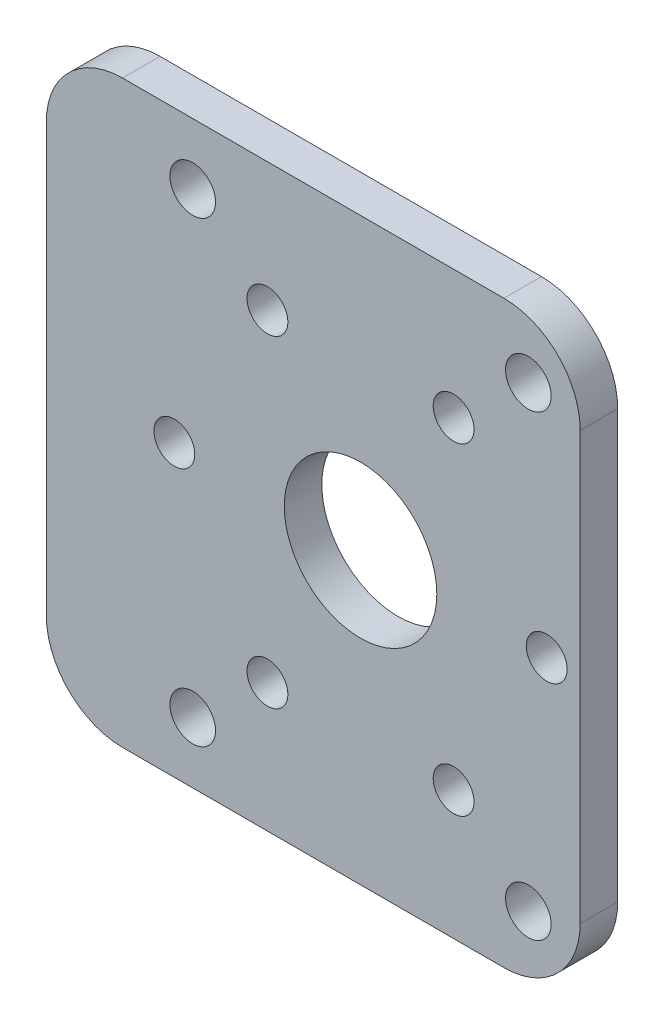
SolidWorks part; units mm, degrees
ref_plane "Front Plane" through (0, 0, 0) normal (0, 0, 1) x (1, 0, 0)
ref_plane "Top Plane" through (0, 0, 0) normal (0, 1, 0) x (1, 0, 0)
ref_plane "Right Plane" through (0, 0, 0) normal (1, 0, 0) x (0, 0, -1)
sketch "Sketch1" plane through (0, 0, 0) normal (0, 0, 1) x (1, 0, 0)
  line L1 (69.85, 48.26) -> (114.3, 48.26)
  line L2 (69.85, 48.26) -> (69.85, 0)
  line L3 (69.85, 0) -> (114.3, 0)
  line L4 (114.3, 48.26) -> (114.3, 0)
  dimension "D1" = 48.26
  dimension "D2" = 44.45
extrude "Boss-Extrude1" add sketch "Sketch1" along normal blind 3.1242
fillet "Fillet1" radius 6.35 4 edges at (114.3, 48.26, 1.5621) (114.3, 0, 1.5621) (69.85, 0, 1.5621) (69.85, 48.26, 1.5621)
hole_wizard "#6 Clearance Hole1" positions "Sketch2" profile "Sketch3" hole size "#6" standard "ANSI Inch"
sketch "Sketch2" plane through (0, 0, 3.1242) normal (0, 0, 1) x (1, 0, 0)
  line L0 (82.042, 43.18) -> (109.982, 43.18) construction
  line L1 (109.982, 43.18) -> (109.982, 5.08) construction
  line L2 (109.982, 5.08) -> (82.042, 5.08) construction
  line L3 (82.042, 5.08) -> (82.042, 43.18) construction
  line L5 (107.95, 48.26) -> (76.2, 48.26) construction
  line L6 (69.85, 41.91) -> (69.85, 6.35) construction
  point P0 (82.042, 43.18)
  point P3 (109.982, 43.18)
  point P6 (109.982, 5.08)
  point P9 (82.042, 5.08)
  point P30 (0, 0)
  point P31 (0, 0)
  point P32 (0, 0)
  point P33 (0, 0)
  dimension "D1" = 38.1
  dimension "D2" = 27.94
  dimension "D3" = 5.08
  dimension "D4" = 12.192
sketch "Sketch3" plane through (82.042, 43.18, 3.1242) normal (1, 0, 0) x (0, -1, 0)
  line L0 (0, 0) -> (0, 6.2208)
  line L1 (0, 6.2208) -> (1.8986, 5.08)
  line L2 (1.8986, 5.08) -> (1.8986, 0)
  line L5 (1.8986, 0) -> (0, 0)
  line L10 (0, 6.2208) -> (-1.8987, 5.08) construction
  line L11 (0, -6.35) -> (0, 107.95) construction
  dimension "Hole Dia." = 3.7973
  dimension "Hole Depth" = 5.08
  dimension "Drill Angle" = 118
sketch "Sketch4" plane through (0, 0, 3.1242) normal (0, 0, 1) x (1, 0, 0)
  line L0 (76.2, 0) -> (107.95, 0) construction
  line L1 (69.85, 41.91) -> (69.85, 6.35) construction
  circle A0 centre (96.012, 24.13) radius 6.35
  point P7 (0, 0)
  dimension "D1" = 12.7
  dimension "D2" = 24.13
  dimension "D3" = 26.162
extrude "Cut-Extrude1" cut sketch "Sketch4" against normal through all
hole_wizard "M3 Clearance Hole1" positions "Sketch5" profile "Sketch6" hole size "M3" standard "ANSI Metric" end condition through all
sketch "Sketch5" plane through (0, 0, 3.1242) normal (0, 0, 1) x (1, 0, 0)
  line L0 (96.012, 24.13) -> (111.512, 24.13) construction
  point P0 (111.512, 24.13)
  point P13 (103.762, 10.7066)
  point P14 (88.262, 10.7066)
  point P15 (80.512, 24.13)
  point P16 (88.262, 37.5534)
  point P17 (103.762, 37.5534)
  point P18 (96.012, 24.13)
  dimension "D1" = 15.5
  dimension "D2" = 6
sketch "Sketch6" plane through (111.512, 24.13, 3.1242) normal (1, 0, 0) x (0, -1, 0)
  line L0 (0, 0) -> (0, 3.1242)
  line L1 (0, 3.1242) -> (1.7, 3.1242)
  line L2 (1.7, 3.1242) -> (1.7, 0)
  line L5 (1.7, 0) -> (0, 0)
  line L11 (0, -6.35) -> (0, 107.95) construction
  dimension "Thru Hole Dia." = 3.4
  dimension "Thru Hole Depth" = 3.1242
